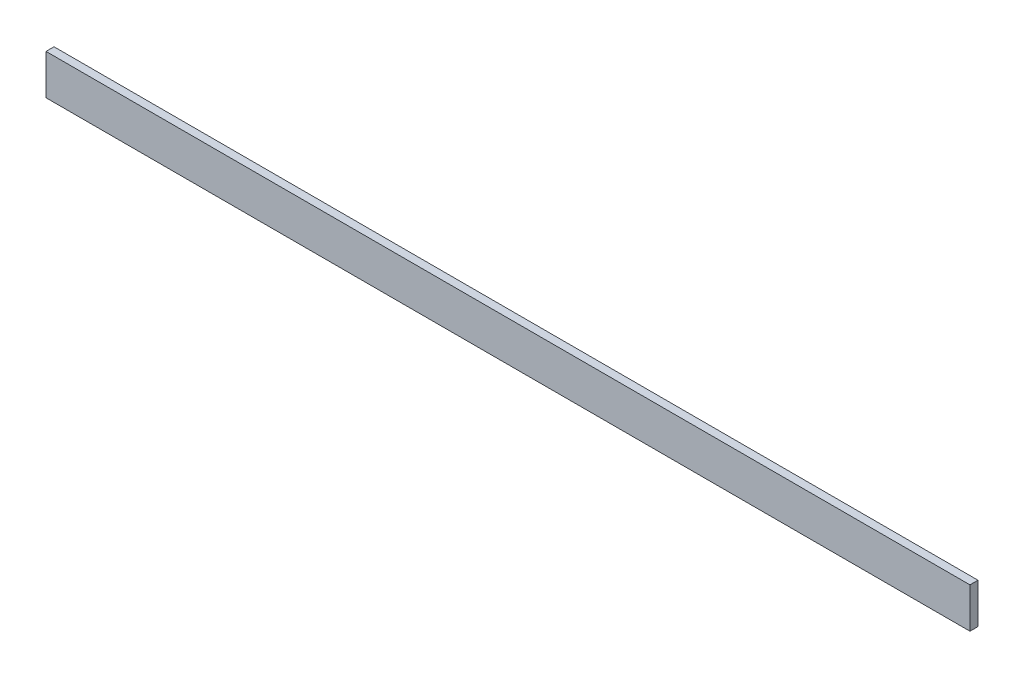
SolidWorks part; units mm, degrees
ref_plane "Спереди" through (0, 0, 0) normal (0, 0, 1) x (1, 0, 0)
ref_plane "Сверху" through (0, 0, 0) normal (0, 1, 0) x (1, 0, 0)
ref_plane "Справа" through (0, 0, 0) normal (1, 0, 0) x (0, 0, -1)
sketch "Эскиз1" plane through (0, 0, 0) normal (0, 0, 1) x (1, 0, 0)
  line L1 (0, 0) -> (460, 0)
  line L2 (0, 0) -> (0, 20)
  line L3 (0, 20) -> (460, 20)
  line L4 (460, 0) -> (460, 20)
extrude "Бобышка-Вытянуть1" add sketch "Эскиз1" along normal blind 4
